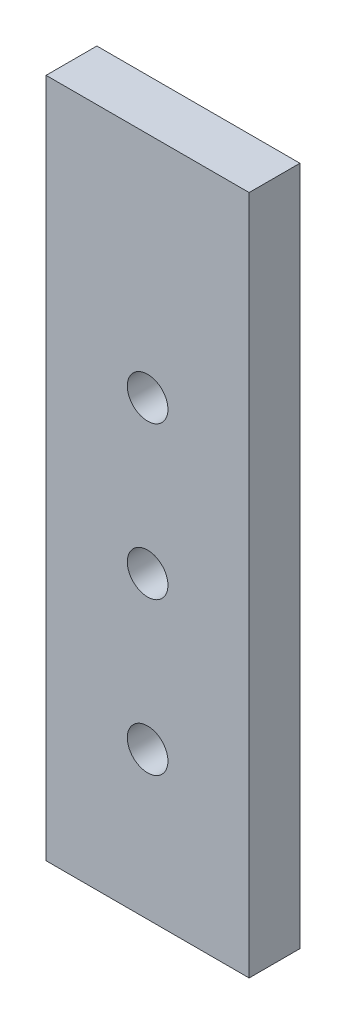
SolidWorks part; units mm, degrees
material "Alloy Steel (SS)"
ref_plane "Front Plane" through (0, 0, 0) normal (0, 0, 1) x (1, 0, 0)
ref_plane "Top Plane" through (0, 0, 0) normal (0, 1, 0) x (1, 0, 0)
ref_plane "Right Plane" through (0, 0, 0) normal (1, 0, 0) x (0, 0, -1)
sketch "Sketch1" plane through (0, 0, 0) normal (0, 0, 1) x (1, 0, 0)
  line L1 (-10, 15) -> (10, 15)
  line L2 (-10, 15) -> (-10, -15)
  line L3 (-10, -15) -> (10, -15)
  line L4 (10, 15) -> (10, -15)
  line L5 (-10, 15) -> (10, -15) construction
  line L6 (-10, -15) -> (10, 15) construction
  point P0 (0, 0)
  dimension "D1" = 20
  dimension "D2" = 30
extrude "Boss-Extrude1" add sketch "Sketch1" along normal blind 5
sketch "Sketch2" plane through (0, 0, 5) normal (0, 0, 1) x (1, 0, 0)
  circle A0 centre (0, 7.5) radius 2
  circle A1 centre (0, -7.5) radius 2
  dimension "D3" = 4
  dimension "D4" = 4
  dimension "D1" = 7.5
  dimension "D2" = 7.5
extrude "Cut-Extrude1" cut sketch "Sketch2" against normal up to vertex (5 mm away) up to point (0, 0, 0)
sketch "Sketch3" plane through (0, -15, 0) normal (0, -1, 0) x (1, 0, 0)
  line L1 (10, 0) -> (-10, 0)
  line L2 (10, 0) -> (10, 5)
  line L3 (10, 5) -> (-10, 5)
  line L4 (-10, 0) -> (-10, 5)
extrude "Boss-Extrude2" add sketch "Sketch3" along normal blind 7
sketch "Sketch4" plane through (0, 15, 0) normal (0, 1, 0) x (1, 0, 0)
  line L7 (-10, 0) -> (10, 0)
  line L8 (-10, 0) -> (-10, -5)
  line L9 (-10, -5) -> (10, -5)
  line L10 (10, 0) -> (10, -5)
extrude "Boss-Extrude3" add sketch "Sketch4" along normal blind 30
sketch "Sketch5" plane through (0, 0, 0) normal (0, 0, -1) x (-1, 0, 0)
  line L0 (0, 130.5) -> (0, -134.7021) construction
  circle A0 centre (0, 22.5) radius 2
  circle A1 centre (0, 7.5) radius 2 construction
  dimension "D1" = 4
  dimension "D2" = 15
extrude "Cut-Extrude2" cut sketch "Sketch5" against normal blind 7
